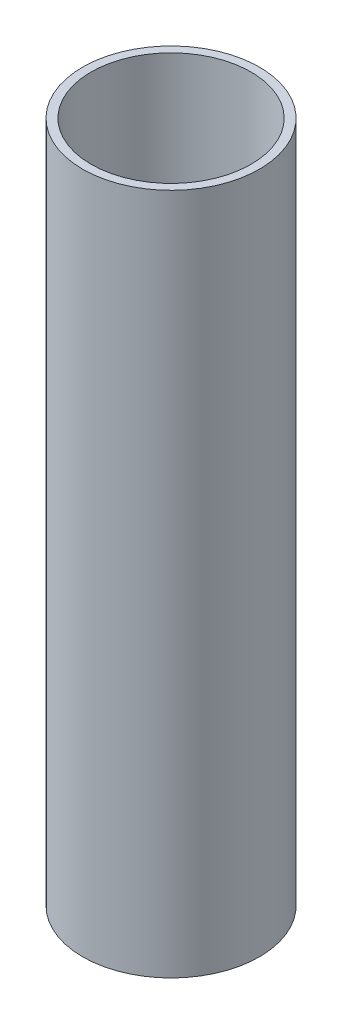
SolidWorks part; units mm, degrees
ref_plane "Front Plane" through (0, 0, 0) normal (0, 0, 1) x (1, 0, 0)
ref_plane "Top Plane" through (0, 0, 0) normal (0, 1, 0) x (1, 0, 0)
ref_plane "Right Plane" through (0, 0, 0) normal (1, 0, 0) x (0, 0, -1)
sketch "Sketch3" plane through (0, 0, 0) normal (0, 1, 0) x (1, 0, 0)
  circle A0 centre (0, 0) radius 21
  circle A1 centre (0, 0) radius 19
extrude "Boss-Extrude1" add sketch "Sketch3" along normal blind 162
